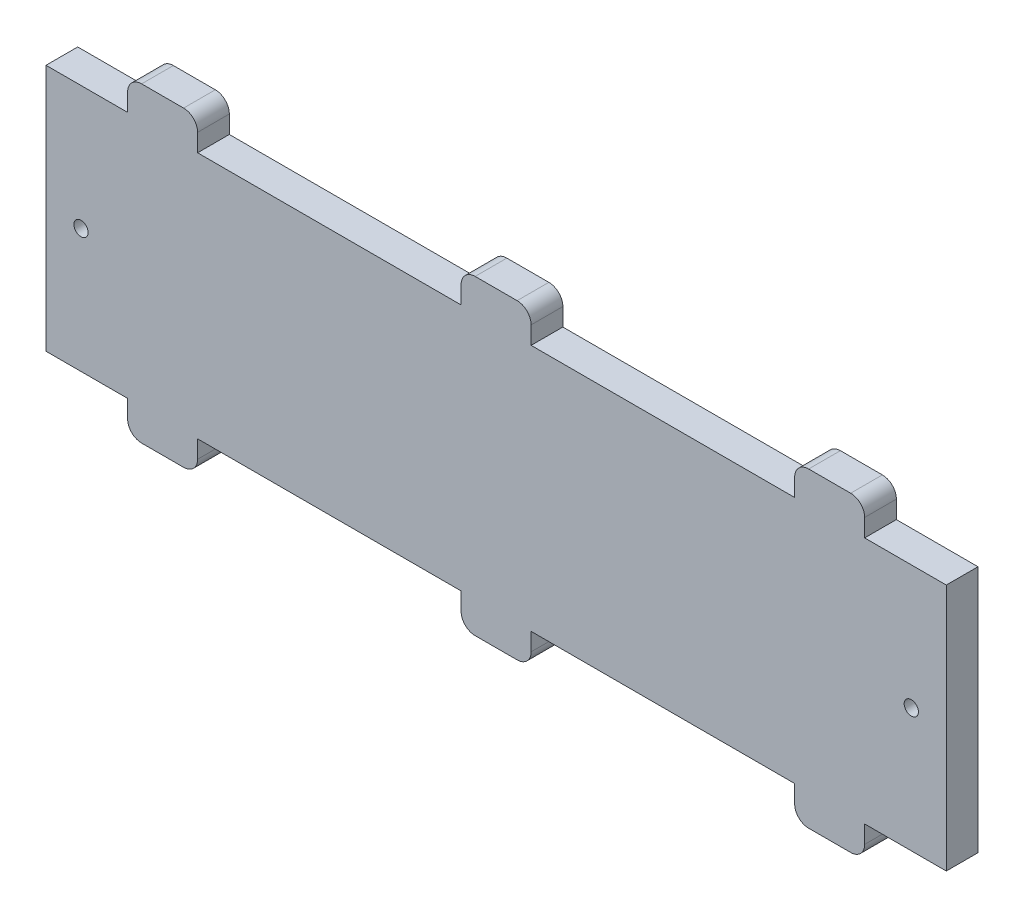
SolidWorks part; units mm, degrees
ref_plane "Front Plane" through (0, 0, 0) normal (0, 0, 1) x (1, 0, 0)
ref_plane "Top Plane" through (0, 0, 0) normal (0, 1, 0) x (1, 0, 0)
ref_plane "Right Plane" through (0, 0, 0) normal (1, 0, 0) x (0, 0, -1)
sketch "Sketch1" plane through (0, 0, 0) normal (0, 0, 1) x (1, 0, 0)
  line L1 (96.5, -26.55) -> (-96.5, -26.55)
  line L2 (96.5, -26.55) -> (96.5, 26.55)
  line L3 (96.5, 26.55) -> (-96.5, 26.55)
  line L4 (-96.5, -26.55) -> (-96.5, 26.55)
  line L5 (96.5, -26.55) -> (-96.5, 26.55) construction
  line L6 (96.5, 26.55) -> (-96.5, -26.55) construction
  point P0 (0, 0)
  dimension "D1" = 193
  dimension "D2" = 53.1
extrude "Boss-Extrude1" add sketch "Sketch1" along normal blind 6.8
sketch "Sketch2" plane through (0, 0, 6.8) normal (0, 0, 1) x (1, 0, 0)
  line L0 (96.5, 26.55) -> (-96.5, 26.55) construction
  line L1 (7.5, 33.35) -> (-7.5, 33.35)
  line L2 (7.5, 33.35) -> (7.5, 26.55)
  line L3 (7.5, 26.55) -> (-7.5, 26.55)
  line L4 (-7.5, 33.35) -> (-7.5, 26.55)
  line L5 (7.5, 33.35) -> (-7.5, 26.55) construction
  line L6 (7.5, 26.55) -> (-7.5, 33.35) construction
  line L7 (-64, 33.35) -> (-79, 33.35)
  line L8 (-64, 33.35) -> (-64, 26.55)
  line L9 (-64, 26.55) -> (-79, 26.55)
  line L10 (-79, 33.35) -> (-79, 26.55)
  line L11 (-64, 33.35) -> (-79, 26.55) construction
  line L12 (-64, 26.55) -> (-79, 33.35) construction
  line L13 (-96.5, 26.55) -> (-96.5, -26.55) construction
  line L14 (-96.5, 0) -> (96.5, 0) construction
  line L15 (96.5, -26.55) -> (96.5, 26.55) construction
  line L16 (-64, -26.55) -> (-79, -33.35) construction
  line L17 (-64, -33.35) -> (-79, -26.55) construction
  line L18 (7.5, -26.55) -> (-7.5, -33.35) construction
  line L19 (7.5, -33.35) -> (-7.5, -26.55) construction
  line L20 (-79, -33.35) -> (-79, -26.55)
  line L21 (-64, -26.55) -> (-79, -26.55)
  line L22 (-64, -33.35) -> (-64, -26.55)
  line L23 (-64, -33.35) -> (-79, -33.35)
  line L24 (-7.5, -33.35) -> (-7.5, -26.55)
  line L25 (7.5, -26.55) -> (-7.5, -26.55)
  line L26 (7.5, -33.35) -> (7.5, -26.55)
  line L27 (7.5, -33.35) -> (-7.5, -33.35)
  point P0 (0, 29.95)
  point P5 (-71.5, 29.95)
  point P27 (-71.5, -29.95)
  point P28 (0, -29.95)
  dimension "D1" = 15
  dimension "D2" = 6.8
  dimension "D3" = 17.5
extrude "Boss-Extrude2" add sketch "Sketch2" against normal blind 6.8
sketch "Sketch3" plane through (0, 0, 6.8) normal (0, 0, 1) x (1, 0, 0)
  line L0 (-96.5, 26.55) -> (-96.5, -26.55) construction
  circle A0 centre (-89, 0) radius 1.524
  dimension "D1" = 3.048
  dimension "D2" = 7.5
extrude "Cut-Extrude1" cut sketch "Sketch3" against normal blind 6.8
fillet "Fillet1" radius 3 8 edges at (7.5, 33.35, 3.4) (-7.5, 33.35, 3.4) (-64, 33.35, 3.4) (-79, 33.35, 3.4) (7.5, -33.35, 3.4) (-7.5, -33.35, 3.4) (-64, -33.35, 3.4) (-79, -33.35, 3.4)
mirror "Mirror1" about plane through (0, 0, 0) normal (1, 0, 0) of "Cut-Extrude1", "Boss-Extrude2", "Fillet1"
